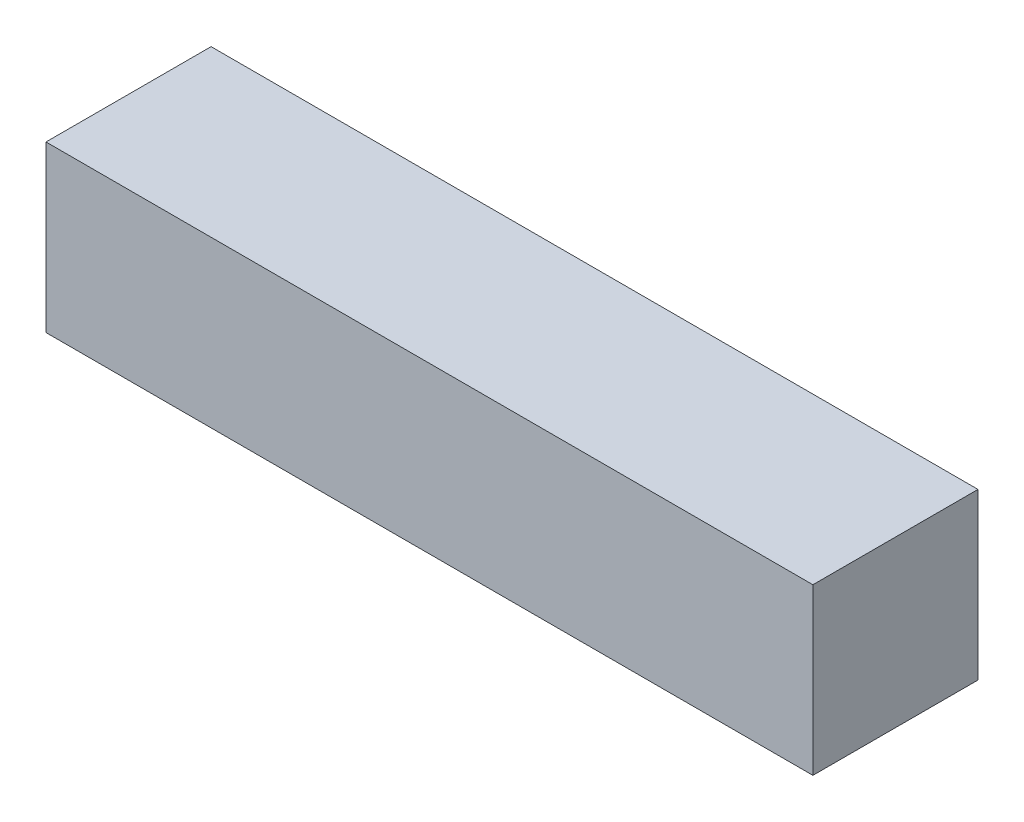
SolidWorks part; units mm, degrees
ref_plane "Front Plane" through (0, 0, 0) normal (0, 0, 1) x (1, 0, 0)
ref_plane "Top Plane" through (0, 0, 0) normal (0, 1, 0) x (1, 0, 0)
ref_plane "Right Plane" through (0, 0, 0) normal (1, 0, 0) x (0, 0, -1)
sketch "Sketch1" plane through (0, 0, 0) normal (1, 0, 0) x (0, 0, -1)
  line L1 (-1.55, -1.55) -> (1.55, -1.55)
  line L2 (-1.55, -1.55) -> (-1.55, 1.55)
  line L3 (-1.55, 1.55) -> (1.55, 1.55)
  line L4 (1.55, -1.55) -> (1.55, 1.55)
  line L5 (-1.55, -1.55) -> (1.55, 1.55) construction
  line L6 (-1.55, 1.55) -> (1.55, -1.55) construction
  point P0 (0, 0)
  dimension "D1" = 3.1
extrude "Boss-Extrude1" add sketch "Sketch1" along normal mid plane 14.4
